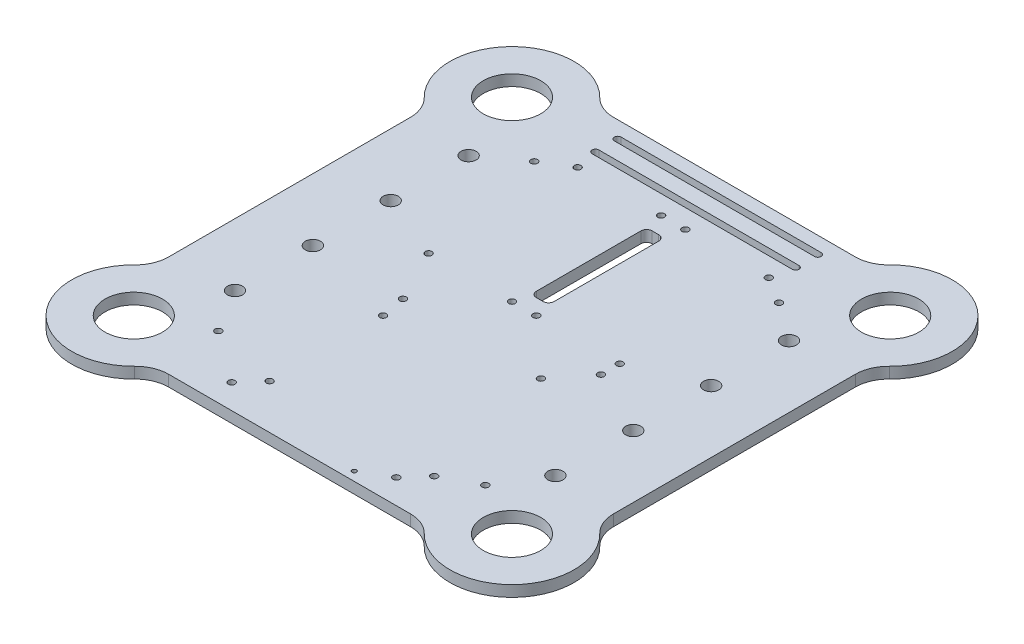
SolidWorks part; units mm, degrees
material "Acrylic (Medium-high impact)"
ref_plane "Front Plane" through (0, 0, 0) normal (0, 0, 1) x (1, 0, 0)
ref_plane "Top Plane" through (0, 0, 0) normal (0, 1, 0) x (1, 0, 0)
ref_plane "Right Plane" through (0, 0, 0) normal (1, 0, 0) x (0, 0, -1)
sketch "Sketch1" plane through (0, 0, 0) normal (0, 1, 0) x (1, 0, 0)
  line L0 (0, -55) -> (0, 55) construction
  line L1 (0, 92.5) -> (45, 92.5) construction
  line L2 (-270.4419, 0) -> (243.27, 0) construction
  line L3 (-55, 0) -> (55, 0) construction
  line L4 (0, 100) -> (54.3339, 100)
  line L5 (100, -54.3339) -> (100, 54.3339)
  line L6 (0, -100) -> (0, 81)
  line L7 (0, -100) -> (54.3339, -100)
  line L8 (0, 94) -> (45, 94)
  line L9 (0, 91) -> (45, 91)
  line L10 (0, 82.5) -> (45, 82.5) construction
  line L11 (0, 84) -> (45, 84)
  line L12 (0, 81) -> (45, 81)
  line L13 (0, 94) -> (0, 100)
  line L14 (0, 84) -> (0, 91)
  circle A0 centre (85, 85) radius 12.9
  circle A1 centre (85, 85) radius 80 construction
  arc A2 (104.5105, 65.0563) -> (65.0563, 104.5105) centre (85, 85) ccw
  arc A3 (54.3339, 100) -> (65.0563, 104.5105) centre (54.3339, 115) ccw
  arc A4 (100, 54.3339) -> (104.5105, 65.0563) centre (115, 54.3339) cw
  arc A6 (45, 91) -> (45, 94) centre (45, 92.5) ccw
  arc A8 (45, 81) -> (45, 84) centre (45, 82.5) ccw
  arc A15 (100, -54.3339) -> (104.5105, -65.0563) centre (115, -54.3339) ccw
  arc A16 (54.3339, -100) -> (65.0563, -104.5105) centre (54.3339, -115) cw
  arc A17 (104.5105, -65.0563) -> (65.0563, -104.5105) centre (85, -85) cw
  circle A18 centre (85, -85) radius 80 construction
  circle A19 centre (85, -85) radius 12.9
  point P13 (8.2159, 90)
  point P23 (8.2159, 80)
  dimension "D1" = 25.8
  dimension "D2" = 15
  dimension "D3" = 200
  dimension "D4" = 160
  dimension "D5" = 100
  dimension "D6" = 0
  dimension "D7" = 1.5
  dimension "D8" = 45
  dimension "D9" = 10
  dimension "D10" = 7.5
extrude "Base" add sketch "Sketch1" along normal blind 5
mirror "Mirror1" about plane through (0, 0, 0) normal (1, 0, 0) of "Base"
sketch "Sketch2" plane through (0, 5, 0) normal (0, 1, 0) x (1, 0, 0)
  line L0 (54.3339, 100) -> (-54.3339, 100) construction
  line L1 (-54.3339, -100) -> (54.3339, -100) construction
  line L2 (0, -2.75) -> (0, 2.75) construction
  circle A0 centre (-42.96, 72.46) radius 1.5
  circle A1 centre (-5.46, 72.46) radius 1.5
  circle A2 centre (5.46, 72.46) radius 1.5
  circle A3 centre (42.96, 72.46) radius 1.5
  circle A4 centre (72.0096, 52.5) radius 3.4
  circle A5 centre (-28.9862, -79.9862) radius 1.5
  circle A6 centre (72.0096, -17.5) radius 3.4
  circle A7 centre (72.0096, -52.5) radius 3.4
  circle A8 centre (42.96, 5.46) radius 1.5
  circle A9 centre (42.96, -2.9862) radius 1.5
  circle A10 centre (5.46, 5.46) radius 1.5
  circle A11 centre (-5.46, 5.46) radius 1.5
  circle A12 centre (-28.9862, -28.9862) radius 1.5
  circle A13 centre (-42.96, 5.46) radius 1.5
  circle A14 centre (-72.0096, 52.5) radius 3.4
  circle A15 centre (-72.0096, -17.5) radius 3.4
  circle A16 centre (-72.0096, -52.5) radius 3.4
  circle A17 centre (45.0138, -79.9862) radius 1.5
  circle A18 centre (36.9998, -89) radius 1.5
  circle A19 centre (-37.0002, -89) radius 1.5
  circle A20 centre (-72.0096, 17.5) radius 3.4
  circle A21 centre (72.0096, 17.5) radius 3.4
  circle A22 centre (25.1, -96) radius 1
  dimension "D1" = 6.8
  dimension "D8" = 2
  dimension "D2" = 37.5
  dimension "D3" = 10.92
  dimension "D4" = 37.5
  dimension "D5" = 35
  dimension "D6" = 70
  dimension "D7" = 47.5
  dimension "D9" = 4
  dimension "D10" = 25.1
extrude "Cut-Extrude1" cut sketch "Sketch2" against normal through all contours A15 | A14 | A0 | A1 | A2 | A3 | A11 | A10 | A13 | A8 | A9 | A12 | A16 | A19 | A5 | A18 | A17 | A7 | A6 | A4 | A20 | A21 | A22
sketch "Sketch3" plane through (0, 5, 0) normal (0, 1, 0) x (1, 0, 0)
  line L0 (0, 64.46) -> (1.5, 64.46)
  line L1 (0, -2.75) -> (0, 2.75) construction
  line L2 (4, 61.96) -> (4, 14.96)
  line L3 (1.5, 12.46) -> (-1.5, 12.46)
  line L4 (-4, 14.96) -> (-4, 61.96)
  line L5 (-1.5, 64.46) -> (0, 64.46)
  circle A0 centre (-5.46, 72.46) radius 1.5 construction
  arc A1 (4, 14.96) -> (1.5, 12.46) centre (1.5, 14.96) cw
  arc A2 (-1.5, 12.46) -> (-4, 14.96) centre (-1.5, 14.96) cw
  arc A3 (1.5, 64.46) -> (4, 61.96) centre (1.5, 61.96) cw
  arc A4 (-4, 61.96) -> (-1.5, 64.46) centre (-1.5, 61.96) cw
  point P13 (-4, 12.46)
  point P18 (-4, 64.46)
  dimension "D2" = 8
  dimension "D4" = 2.5
  dimension "D1" = 52
  dimension "D3" = 8
extrude "Cut-Extrude2" cut sketch "Sketch3" against normal through all
sketch "Sketch4" plane through (0, 5, 0) normal (0, 1, 0) x (1, 0, 0)
  line L0 (54.3339, 100) -> (-54.3339, 100) construction
  line L1 (-54.3339, -100) -> (54.3339, -100) construction
  circle A0 centre (-55.0096, 65) radius 1.5
  circle A1 centre (-72.0096, 52.5) radius 3.4 construction
  circle A2 centre (55.0096, 65) radius 1.5
  circle A3 centre (72.0096, 52.5) radius 3.4 construction
  circle A4 centre (-60.0096, -72) radius 1.5
  circle A5 centre (-72.0096, -52.5) radius 3.4 construction
  circle A6 centre (60.0096, -72) radius 1.5
  circle A7 centre (72.0096, -52.5) radius 3.4 construction
  circle A8 centre (31.0096, -18) radius 1.5
  circle A9 centre (-31.0096, -18) radius 1.5
  dimension "D1" = 3
  dimension "D6" = 12
  dimension "D8" = 3
  dimension "D12" = 29
  dimension "D2" = 35
  dimension "D3" = 17
  dimension "D4" = 35
  dimension "D5" = 17
  dimension "D7" = 28
  dimension "D9" = 28
  dimension "D10" = 12
  dimension "D11" = 82
  dimension "D13" = 82
  dimension "D14" = 29
extrude "Cut-Extrude3" cut sketch "Sketch4" against normal through all
